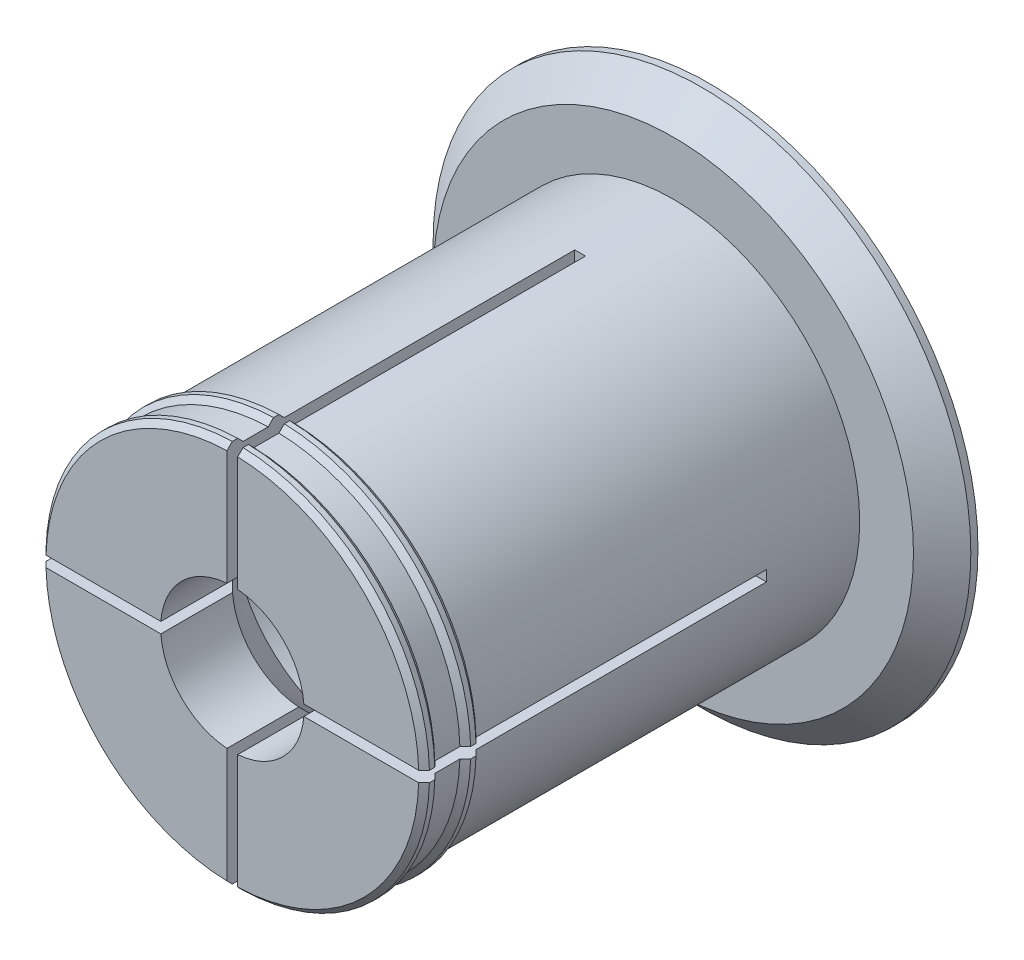
SolidWorks part; units mm, degrees
ref_plane "Front" through (0, 0, 0) normal (0, 0, 1) x (1, 0, 0)
ref_plane "Top" through (0, 0, 0) normal (0, 1, 0) x (1, 0, 0)
ref_plane "Right" through (0, 0, 0) normal (1, 0, 0) x (0, 0, -1)
sketch "Axle base sketch" plane through (0, 0, 0) normal (0, 0, 1) x (1, 0, 0)
  circle A0 centre (0, 0) radius 26
  dimension "D1" = 52
extrude "Axle" add sketch "Axle base sketch" along normal blind 61.5
sketch "Guard base" plane through (0, 0, 0) normal (0, 0, -1) x (-1, 0, 0)
  circle A0 centre (0, 0) radius 37.5
  dimension "D1" = 75
extrude "Guard" add sketch "Guard base" along normal blind 5
sketch "Inner axle hole base" plane through (0, 0, 61.5) normal (0, 0, 1) x (1, 0, 0)
  circle A0 centre (0, 0) radius 10
  dimension "D1" = 20
extrude "Inner axle hole" cut sketch "Inner axle hole base" against normal through all
sketch "Mate ring base" plane through (0, 0, 0) normal (0, 1, 0) x (1, 0, 0)
  line L0 (26, -61.5) -> (26.75, -60.75)
  line L1 (26.75, -60.75) -> (26.75, -60)
  line L2 (26.75, -60) -> (26, -59.25)
  line L3 (26.75, -60.75) -> (26.75, -61.5) construction
  line L4 (26.75, -61.5) -> (26, -61.5) construction
  line L5 (26, -59.25) -> (26, -61.5)
  line L6 (26, -61.5) -> (26, 0) construction
  line L8 (26, -55.75) -> (26.75, -55)
  line L9 (26.75, -55) -> (26.75, -54.25)
  line L10 (26.75, -54.25) -> (26, -53.5)
  line L11 (26, -53.5) -> (26, -55.75)
  dimension "D1" = 0.75
  dimension "D2" = 0.75
  dimension "D3" = 5
  dimension "D4" = 0.75
ref_axis "Center Z" through (0, 0, 0) along (0, 0, -1)
revolve "Mate rings" add sketch "Mate ring base" angle 360 about axis through (0, 0, 0) along (0, 0, -1)
sketch "Inner mass remove base" plane through (0, 0, 0) normal (1, 0, 0) x (0, 0, -1)
  line L0 (-61.5, 0) -> (-43.5, -18)
  line L1 (-43.5, -18) -> (-13, -18)
  line L2 (-13, -18) -> (5, 0)
  line L3 (5, 0) -> (-61.5, 0)
  line L4 (5, -10) -> (5, 10) construction
  line L5 (-43.5, -18) -> (-43.5, -10) construction
  line L6 (-43.5, -18) -> (-43.5, -26) construction
  line L7 (-61.5, 10) -> (-61.5, -10) construction
  point P9 (-61.5, -10)
  point P11 (-61.5, -26)
  dimension "D1" = 135
revolve "Inner mass remove" cut sketch "Inner mass remove base" angle 360 about axis through (0, 0, 0) along (0, 0, -1)
ref_point "Bend room endpoint"
sketch "Bend room base" plane through (0, 0, 61.5) normal (0, 0, 1) x (1, 0, 0)
  line L0 (0.75, -37.5) -> (0.75, 37.5)
  line L1 (0.75, 37.5) -> (-0.75, 37.5)
  line L2 (-0.75, 37.5) -> (-0.75, -37.5)
  line L3 (-0.75, -37.5) -> (0.75, -37.5)
  dimension "D1" = 0.75
  dimension "D2" = 0.75
  dimension "D3" = 37.5
  dimension "D4" = 37.5
extrude "Bend room 1" cut sketch "Bend room base" against normal up to vertex (28.9925 mm away)
pattern_circular "Bend room 2" count 2 every 90 about axis through (0, 0, 0) along (0, 0, -1) of "Bend room 1"
chamfer "Easy removal chamfer" distance 4 angle 45 1 edges at (-37.5, 0, 0)
equation "\"32_92_spool_inner_diameter\"=32"
equation "\"D1@Axle base sketch\"=\"53_55_spool_inner_diameter\"- \"spool_inner_diameter_room\""
equation "\"spool_inner_diameter_room\"=1"
equation "\"32_92_spool_thickness\"=92"
equation "\"D1@Axle\"=\"53_55_spool_thickness\"+\"guard_thickness\"+\"removal_room\"*2"
equation "\"32_92_guard_diameter\"=50"
equation "\"D1@Guard base\"=\"53_55_guard_diameter\""
equation "\"guard_thickness\"=5"
equation "\"D1@Guard\"=\"guard_thickness\""
equation "\"large_inner_axle_diameter\"=20"
equation "\"D1@Inner axle hole base\"=\"large_inner_axle_diameter\""
equation "\"mate_room\"= 0.25"
equation "\"removal_room\"= 0.75"
equation "\"small_inner_axle_diameter\"=17"
equation "\"53_55_spool_inner_diameter\"=53"
equation "\"53_55_spool_thickness\"=55"
equation "\"53_55_guard_diameter\"=75"
equation "\"D1@Mate ring base\"=\"removal_room\""
equation "\"D2@Mate ring base\"=\"removal_room\""
equation "\"D3@Mate ring base\"=\"guard_thickness\""
equation "\"D4@Mate ring base\"=\"removal_room\""
equation "\"D1@Bend room base\" = \"removal_room\""
equation "\"D2@Bend room base\"=\"removal_room\""
equation "\"D3@Bend room base\"=\"53_55_guard_diameter\"/2"
equation "\"D4@Bend room base\"=\"53_55_guard_diameter\"/2"
equation "\"bend_room_length_multiplier\"=3"
equation "\"D1@Easy removal chamfer\"=\"guard_thickness\"-1"
equation "\"32_92_extra_spool_thickness\"=-5"
equation "\"39_92_spool_inner_diameter\"=39"
equation "\"39_92_spool_thickness\"=92"
equation "\"39_92_guard_diameter\"=60"
equation "\"53_55_bend_room_length_multiplier\"=1.5"
